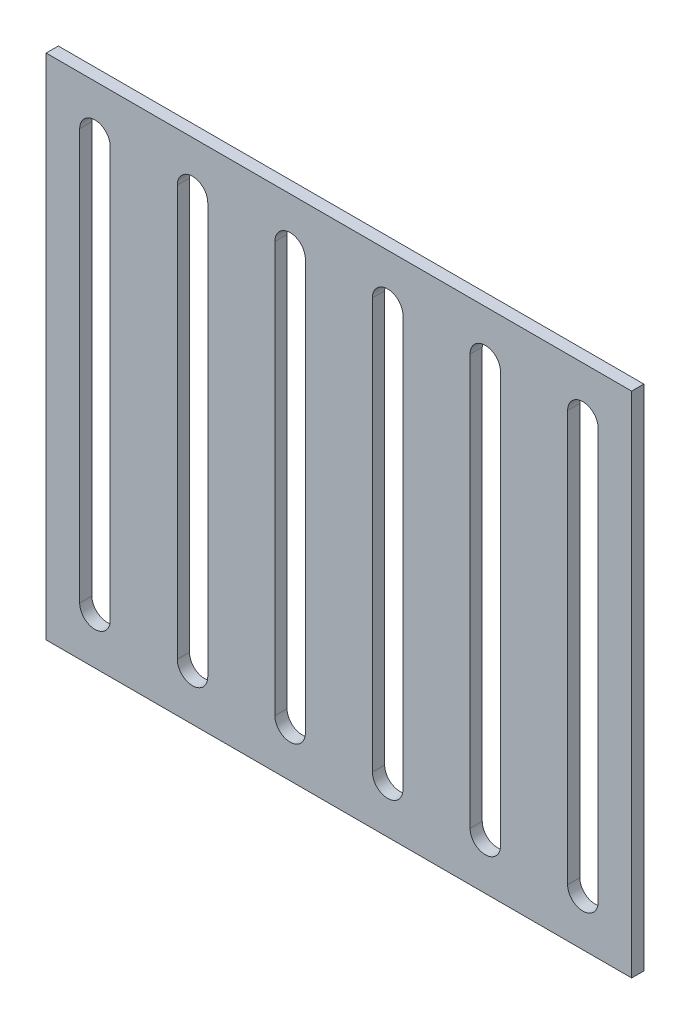
SolidWorks part; units mm, degrees
ref_plane "Front Plane" through (0, 0, 0) normal (0, 0, 1) x (1, 0, 0)
ref_plane "Top Plane" through (0, 0, 0) normal (0, 1, 0) x (1, 0, 0)
ref_plane "Right Plane" through (0, 0, 0) normal (1, 0, 0) x (0, 0, -1)
sketch "Sketch1" plane through (0, 0, 0) normal (0, 0, 1) x (1, 0, 0)
  line L1 (0, 0) -> (288, 0)
  line L2 (0, 0) -> (0, 250)
  line L3 (0, 250) -> (288, 250)
  line L4 (288, 0) -> (288, 250)
  dimension "D1" = 250
  dimension "D2" = 288
extrude "Boss-Extrude1" add sketch "Sketch1" along normal blind 6
sketch "Sketch2" plane through (0, 0, 6) normal (0, 0, 1) x (1, 0, 0)
  line L0 (0, 250) -> (0, 0) construction
  line L9 (0, 0) -> (288, 0) construction
  line L10 (24, 24) -> (24, 226) construction
  line L11 (16.5, 24) -> (16.5, 226)
  line L12 (31.5, 24) -> (31.5, 226)
  line L13 (288, 250) -> (0, 250) construction
  arc A1 (16.5, 24) -> (31.5, 24) centre (24, 24) ccw
  arc A2 (31.5, 226) -> (16.5, 226) centre (24, 226) ccw
  point P7 (24, 125)
  dimension "D3" = 24
  dimension "D4" = 7.5
  dimension "D1" = 24
  dimension "D2" = 24
extrude "Cut-Extrude1" cut sketch "Sketch2" against normal through all
pattern_linear "LPattern4" count 6 spacing 48 along (1, 0, 0) of "Cut-Extrude1"
